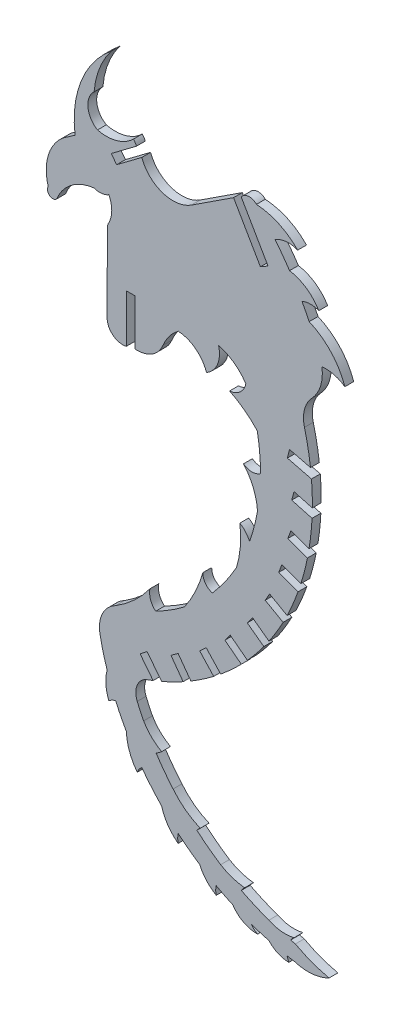
SolidWorks part; units mm, degrees
ref_plane "Front Plane" through (0, 0, 0) normal (0, 0, 1) x (1, 0, 0)
ref_plane "Top Plane" through (0, 0, 0) normal (0, 1, 0) x (1, 0, 0)
ref_plane "Right Plane" through (0, 0, 0) normal (1, 0, 0) x (0, 0, -1)
sketch "Sketch1" plane through (0, 0, 0) normal (0, 0, 1) x (1, 0, 0)
  line L5 (-19.6025, -30.4046) -> (-17.1824, -33.0184)
  line L6 (-21.12, -35.6797) -> (-23.3181, -32.6558)
  line L7 (-23.3181, -32.6558) -> (-24.552, -33.5529)
  line L8 (-24.552, -33.5529) -> (-22.4518, -36.4439)
  line L9 (-26.1665, -38.264) -> (-28.6769, -35.0501)
  line L10 (-28.6769, -35.0501) -> (-29.879, -35.9899)
  line L11 (-29.879, -35.9899) -> (-27.6338, -38.866)
  line L12 (-27.6338, -38.866) -> (-28.9299, -39.3453)
  line L13 (-30.7393, 9.1132) -> (-30.7394, 17.0638)
  line L14 (-30.7394, 17.0638) -> (-32.2634, 17.0638)
  line L15 (-32.2634, 17.0638) -> (-32.2634, 8.7613)
  line L16 (-35.5731, 11.3846) -> (-35.5279, 24.7622)
  line L17 (-43.2054, 34.42) -> (-41.0981, 35.8997)
  line L18 (-30.5073, 39.549) -> (-34.8504, 36.2875)
  line L19 (-34.8504, 36.2875) -> (-33.9344, 35.0666)
  line L20 (-33.9344, 35.0666) -> (-29.5909, 38.3281)
  line L21 (-21.0404, 35.4786) -> (-13.7549, 40.2356)
  line L22 (-13.7549, 40.2356) -> (-9.1213, 32.2252)
  line L23 (-9.1213, 32.2252) -> (-7.802, 32.9882)
  line L24 (-7.802, 32.9882) -> (-12.4336, 40.9986)
  line L25 (-0.4799, 6.5351) -> (-4.0923, 7.4449)
  line L26 (-4.0923, 7.4449) -> (-4.4639, 5.9656)
  line L27 (-4.4639, 5.9656) -> (-0.3111, 4.9195)
  line L28 (-0.1634, 0.6634) -> (-3.3194, 1.5278)
  line L29 (-3.3194, 1.5278) -> (-3.7227, 0.0554)
  line L30 (-3.7227, 0.0554) -> (-0.2138, -0.9043)
  line L31 (-0.7309, -5.7098) -> (-3.8559, -4.5652)
  line L32 (-3.8559, -4.5652) -> (-4.3804, -5.9988)
  line L33 (-4.3804, -5.9988) -> (-1.0086, -7.2337)
  line L34 (-2.1471, -11.6495) -> (-5.4156, -10.4277)
  line L35 (-5.4156, -10.4277) -> (-5.9521, -11.8564)
  line L36 (-5.9521, -11.8564) -> (-2.6319, -13.0992)
  line L37 (-4.5137, -17.5871) -> (-7.5337, -15.867)
  line L38 (-7.5337, -15.867) -> (-8.2888, -17.1933)
  line L39 (-8.2888, -17.1933) -> (-5.207, -18.9468)
  line L40 (-7.6452, -22.9813) -> (-10.4824, -20.895)
  line L41 (-10.4824, -20.895) -> (-11.3884, -22.124)
  line L42 (-11.3884, -22.124) -> (-8.5272, -24.2291)
  line L43 (-11.3676, -27.6968) -> (-14.3172, -25.4263)
  line L44 (-14.3172, -25.4263) -> (-15.2491, -26.6343)
  line L45 (-15.2491, -26.6343) -> (-12.4196, -28.814)
  line L46 (-15.9812, -32.0721) -> (-18.4838, -29.3684)
  line L47 (-18.4838, -29.3684) -> (-19.6025, -30.4046)
  arc A0 (-43.2054, 34.42) -> (-45.7292, 25.885) centre (-37.9891, 28.2369) ccw
  arc A1 (-45.7292, 25.885) -> (-44.2929, 24.7622) centre (-44.9486, 25.4036) ccw
  arc A2 (-44.2929, 24.7622) -> (-37.8208, 29.6429) centre (-36.9702, 21.7834) cw
  arc A3 (-37.8208, 29.6429) -> (-35.2685, 29.9191) centre (-36.8274, 32.3933) ccw
  arc A4 (-35.2685, 25.7497) -> (-35.2685, 29.9191) centre (-39.3616, 27.8344) ccw
  arc A7 (-9.803, 41.2082) -> (-2.6945, 37.9183) centre (-10.428, 30.533) cw
  arc A8 (-2.6945, 37.9183) -> (-6.5667, 37.5431) centre (-4.2824, 34.1375) ccw
  arc A9 (-4.0923, 34.1603) -> (0.9527, 30.696) centre (-5.2703, 27.039) cw
  arc A10 (-21.12, -35.6797) -> (-17.1824, -33.0184) centre (-43.2354, 1.2863) ccw
  arc A11 (-26.1665, -38.264) -> (-22.4518, -36.4439) centre (-43.2402, 1.284) ccw
  arc A12 (-28.9299, -39.3453) -> (-30.3761, -43.3445) centre (-27.5002, -42.1234) ccw
  arc A13 (-30.3761, -43.3445) -> (-29.2733, -45.7151) centre (5.1197, -28.273) ccw
  arc A14 (-34.0936, -45.1232) -> (-32.2634, -48.7518) centre (2.7252, -28.8281) ccw
  arc A15 (-36.8049, -36.4782) -> (-35.5731, -41.2535) centre (2.7252, -28.8281) ccw
  arc A16 (-34.0936, -30.8968) -> (-36.8049, -36.4782) centre (-31.7267, -35.4958) ccw
  arc A17 (-27.1849, -28.2766) -> (-22.2191, -25.1488) centre (-42.3627, 1.3257) ccw
  arc A18 (-11.6392, 13.4859) -> (-16.3452, 16.8716) centre (-18.4183, 9.0265) ccw
  arc A19 (-30.7393, 9.1132) -> (-25.9323, 12.0896) centre (-30.3794, 13.9017) ccw
  arc A20 (-35.5731, 11.3846) -> (-32.2634, 8.7613) centre (-32.8866, 11.3746) ccw
  arc A21 (-35.2685, 25.7497) -> (-35.5279, 24.7622) centre (-33.5657, 24.7745) ccw
  arc A22 (0.9527, 30.696) -> (-1.9542, 30.6544) centre (-0.45, 27.1344) ccw
  arc A23 (-0.6999, 28.2369) -> (5.4541, 21.5904) centre (-5.1566, 17.9383) cw
  arc A24 (-30.5073, 39.549) -> (-31.0246, 40.3534) centre (-32.8478, 38.6124) ccw
  arc A25 (-29.5909, 38.3281) -> (-21.0404, 35.4786) centre (-24.1852, 40.2955) ccw
  arc A26 (-9.803, 41.2082) -> (-12.4336, 40.9986) centre (-11.0312, 40.0111) ccw
  arc A27 (-0.6999, 28.2369) -> (-1.9542, 30.6544) centre (-45.2247, 6.6697) ccw
  arc A28 (-0.2483, 17.0116) -> (1.4848, 22.6045) centre (-5.1334, 21.5904) ccw
  arc A29 (-0.2483, 17.0116) -> (-1.5218, 12.0329) centre (3.6447, 13.3635) ccw
  arc A30 (-0.4799, 6.5351) -> (-1.5218, 12.0329) centre (-43.2341, 1.2801) ccw
  arc A31 (-0.1634, 0.6634) -> (-0.3111, 4.9195) centre (-43.2358, 1.2993) ccw
  arc A32 (-0.7309, -5.7098) -> (-0.2138, -0.9043) centre (-43.2345, 1.2943) ccw
  arc A33 (-2.1471, -11.6495) -> (-1.0086, -7.2337) centre (-43.2322, 1.2986) ccw
  arc A34 (-4.5137, -17.5871) -> (-2.6319, -13.0992) centre (-43.2351, 1.287) ccw
  arc A35 (-7.6452, -22.9813) -> (-5.207, -18.9468) centre (-43.2376, 1.2826) ccw
  arc A36 (-11.3676, -27.6968) -> (-8.5272, -24.2291) centre (-43.2269, 1.2966) ccw
  arc A37 (-15.9812, -32.0721) -> (-12.4196, -28.814) centre (-43.2304, 1.2908) ccw
  arc A38 (5.4541, 21.5904) -> (1.4848, 22.6045) centre (2.1131, 16.7887) ccw
  arc A39 (-4.0923, 34.1603) -> (-6.5667, 37.5431) centre (-45.2247, 6.6697) ccw
  arc A40 (-35.5731, -41.2535) -> (-35.2685, -45.7151) centre (-28.6416, -43.0215) ccw
  arc A41 (-35.2685, -45.7151) -> (-34.0936, -45.1232) centre (-33.6897, -47.3871) cw
  arc A42 (-32.2634, -48.7518) -> (-30.3761, -53.9345) centre (-23.1368, -48.3633) ccw
  arc A43 (-30.3761, -53.9345) -> (-29.5878, -52.8494) centre (-28.0828, -54.7717) cw
  arc A44 (-26.1665, -56.8713) -> (-23.3181, -61.0407) centre (-18.5486, -54.7246) ccw
  arc A45 (-23.3181, -61.0407) -> (-23.3181, -59.5348) centre (-19.5076, -60.2878) cw
  arc A46 (-19.6025, -62.3338) -> (-16.7425, -65.5113) centre (-13.2882, -59.5264) ccw
  arc A47 (-16.7425, -65.5113) -> (-16.7425, -64.0724) centre (-13.9273, -64.7919) cw
  arc A48 (-13.8729, -65.5113) -> (-9.5946, -67.7332) centre (-9.7425, -62.7882) ccw
  arc A49 (-9.5946, -67.7332) -> (-10.6935, -66.7899) centre (-8.3215, -65.1387) cw
  arc A50 (-7.6452, -67.7332) -> (-4.2059, -69.2575) centre (-4.2059, -64.615) ccw
  arc A51 (-4.2059, -69.2575) -> (-4.5137, -68.4356) centre (-1.3511, -67.7198) cw
  arc A52 (-3.2728, -68.6424) -> (2.7252, -68.13) centre (-0.8988, -61.0697) ccw
  arc A53 (2.7252, -68.13) -> (-3.0977, -65.9503) centre (7.5237, -46.4439) cw
  arc A54 (-29.5878, -52.8494) -> (-26.1665, -56.8713) centre (2.7252, -28.8281) ccw
  arc A55 (-23.3181, -59.5348) -> (-19.6025, -62.3338) centre (2.7252, -28.8281) ccw
  arc A56 (-16.7425, -64.0724) -> (-13.8729, -65.5113) centre (2.7252, -28.8281) ccw
  arc A57 (-10.6935, -66.7899) -> (-7.6452, -67.7332) centre (2.7252, -28.8281) ccw
  arc A58 (-4.5137, -68.4356) -> (-3.2728, -68.6424) centre (2.7252, -28.8281) ccw
  arc A59 (-29.2733, -45.7151) -> (-26.1665, -48.7518) centre (-22.1911, -41.5772) ccw
  arc A60 (-27.1297, -49.4172) -> (-26.1665, -48.7518) centre (-28.6196, -46.2306) ccw
  arc A61 (-24.1852, -53.3395) -> (-19.5076, -56.8713) centre (-14.8321, -45.8157) ccw
  arc A62 (-20.0874, -57.457) -> (-19.5076, -56.8713) centre (-18.2877, -58.659) cw
  arc A63 (-15.9812, -60.5508) -> (-11.8464, -61.9349) centre (-10.9286, -52.3247) ccw
  arc A64 (-3.8993, -65.7665) -> (-3.3194, -65.1387) centre (-0.9438, -67.9144) cw
  arc A65 (-7.6452, -64.662) -> (-3.3194, -65.1387) centre (-4.8275, -58.9572) ccw
  arc A66 (-12.4221, -62.6153) -> (-11.8464, -61.9349) centre (-8.9141, -64.9997) cw
  arc A67 (-3.8993, -65.7665) -> (-3.0977, -65.9503) centre (5.1197, -28.273) ccw
  arc A68 (-12.4221, -62.6153) -> (-7.6452, -64.662) centre (5.1197, -28.273) ccw
  arc A69 (-20.0874, -57.457) -> (-15.9812, -60.5508) centre (5.1197, -28.273) ccw
  arc A70 (-27.1297, -49.4172) -> (-24.1852, -53.3395) centre (5.1197, -28.273) ccw
  arc A71 (-34.0936, -30.8968) -> (-28.1834, -25.4263) centre (-45.1331, -13.0422) ccw
  arc A72 (-28.1834, -25.4263) -> (-27.1849, -28.2766) centre (-25.3012, -26.0167) ccw
  arc A73 (-22.2191, -25.1488) -> (-19.0432, -18.4322) centre (-40.7661, -12.2698) ccw
  arc A74 (-19.0432, -18.4322) -> (-17.4006, -20.6643) centre (-16.8405, -18.5317) ccw
  arc A75 (-13.2362, -14.7463) -> (-12.6647, -7.8539) centre (-29.0724, -9.9633) ccw
  arc A76 (-12.6647, -7.8539) -> (-10.9996, -9.7657) centre (-14.7275, -11.3315) cw
  arc A77 (-9.6219, -4.5652) -> (-12.0337, 1.3257) centre (-19.5337, -5.1841) ccw
  arc A78 (-12.0337, 1.3257) -> (-9.0961, 1.3257) centre (-10.5649, 3.2993) ccw
  arc A79 (-23.2946, 15.5123) -> (-18.4183, 11.7726) centre (-23.6784, 9.9629) cw
  arc A80 (-18.4183, 11.7726) -> (-16.3452, 16.8716) centre (-20.6658, 15.6574) ccw
  arc A81 (-9.6638, 7.4449) -> (-14.4395, 11.0097) centre (-21.7404, -3.7525) ccw
  arc A82 (-14.4395, 11.0097) -> (-11.6392, 13.4859) centre (-14.6687, 14.0905) ccw
  arc A83 (-23.2946, 15.5123) -> (-25.9323, 12.0896) centre (-18.4183, 9.0265) ccw
  arc A84 (-9.0961, 1.3257) -> (-9.6638, 7.4449) centre (-42.3627, 1.3257) ccw
  arc A85 (-10.9996, -9.7657) -> (-9.6219, -4.5652) centre (-42.3627, 1.3257) ccw
  arc A86 (-17.4006, -20.6643) -> (-13.2362, -14.7463) centre (-42.3627, 1.3257) ccw
  arc A87 (-41.0981, 35.8997) -> (-34.8504, 51.5865) centre (-24.0517, 38.1981) cw
  arc A88 (-34.8504, 51.5865) -> (-37.8208, 44.0069) centre (-23.6431, 42.8226) ccw
  arc A89 (-37.8208, 44.0069) -> (-37.2347, 38.6124) centre (-35.5059, 41.5293) ccw
  arc A90 (-37.2347, 38.6124) -> (-31.0246, 40.3534) centre (-35.693, 45.0594) ccw
extrude "Boss-Extrude1" add sketch "Sketch1" along normal blind 1.524
